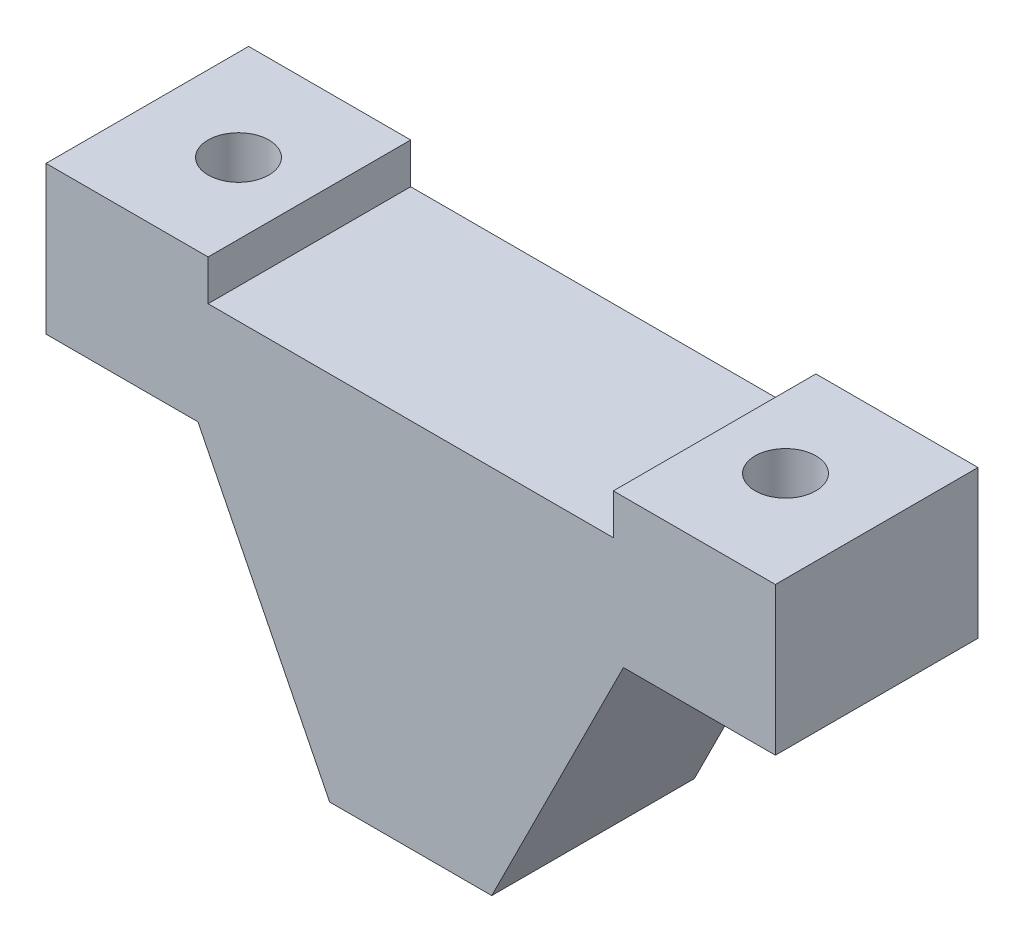
SolidWorks part; units mm, degrees
ref_plane "Front Plane" through (0, 0, 0) normal (0, 0, 1) x (1, 0, 0)
ref_plane "Top Plane" through (0, 0, 0) normal (0, 1, 0) x (1, 0, 0)
ref_plane "Right Plane" through (0, 0, 0) normal (1, 0, 0) x (0, 0, -1)
sketch "Sketch1" plane through (0, 0, 0) normal (0, 0, 1) x (1, 0, 0)
  line L0 (-4, 0) -> (4, 0)
  line L1 (4, 0) -> (10.5, 13)
  line L2 (10.5, 13) -> (18, 13)
  line L3 (18, 13) -> (18, 20.3)
  line L4 (18, 20.3) -> (-18, 20.3)
  line L5 (0, 20.3) -> (0, 0) construction
  line L6 (-18, 13) -> (-18, 20.3)
  line L7 (-10.5, 13) -> (-18, 13)
  line L8 (-4, 0) -> (-10.5, 13)
  dimension "D1" = 4
  dimension "D2" = 13
  dimension "D3" = 18
  dimension "D4" = 7.3
  dimension "D5" = 7.5
extrude "Boss-Extrude1" add sketch "Sketch1" along normal blind 10
sketch "Sketch2" plane through (0, 0, 10) normal (0, 0, 1) x (1, 0, 0)
  line L0 (0, 20.3) -> (0, 0) construction
  line L1 (18, 20.3) -> (-18, 20.3) construction
  line L2 (-10, 18.3) -> (10, 18.3)
  line L3 (10, 18.3) -> (10, 20.3)
  line L4 (10, 20.3) -> (-10, 20.3)
  line L5 (-10, 18.3) -> (-10, 20.3)
  point P10 (0, 18.3)
  dimension "D1" = 10
  dimension "D2" = 2
extrude "Cut-Extrude1" cut sketch "Sketch2" against normal through all
sketch "Sketch3" plane through (0, 20.3, 0) normal (0, 1, 0) x (1, 0, 0)
  line L0 (-18, -5) -> (18, -5) construction
  line L1 (-18, -10) -> (-18, 0) construction
  line L2 (18, -10) -> (18, 0) construction
  line L3 (0, 0) -> (0, -10) construction
  line L4 (-10, 0) -> (10, 0) construction
  line L5 (-10, -10) -> (10, -10) construction
  circle A0 centre (-13.5, -5) radius 1.5
  circle A2 centre (13.5, -5) radius 1.5
  dimension "D2" = 3
  dimension "D3" = 13.5
extrude "Cut-Extrude2" cut sketch "Sketch3" against normal through all and the other way through all
